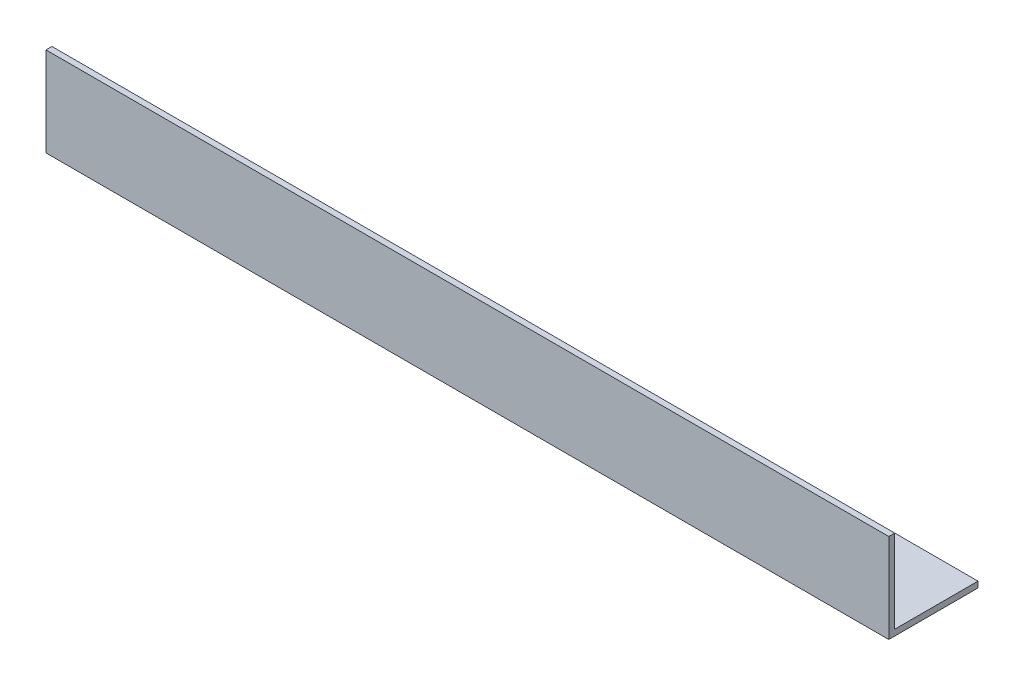
SolidWorks part; units mm, degrees
ref_plane "Спереди" through (0, 0, 0) normal (0, 0, 1) x (1, 0, 0)
ref_plane "Сверху" through (0, 0, 0) normal (0, 1, 0) x (1, 0, 0)
ref_plane "Справа" through (0, 0, 0) normal (1, 0, 0) x (0, 0, -1)
sketch "Эскиз1" plane through (0, 0, 0) normal (1, 0, 0) x (0, 0, -1)
  line L0 (0, 0) -> (0, 45)
  line L1 (0, 0) -> (45, 0)
extrude "Вытянуть-Тонкостенный1" add sketch "Эскиз1" along normal blind 425 thin
